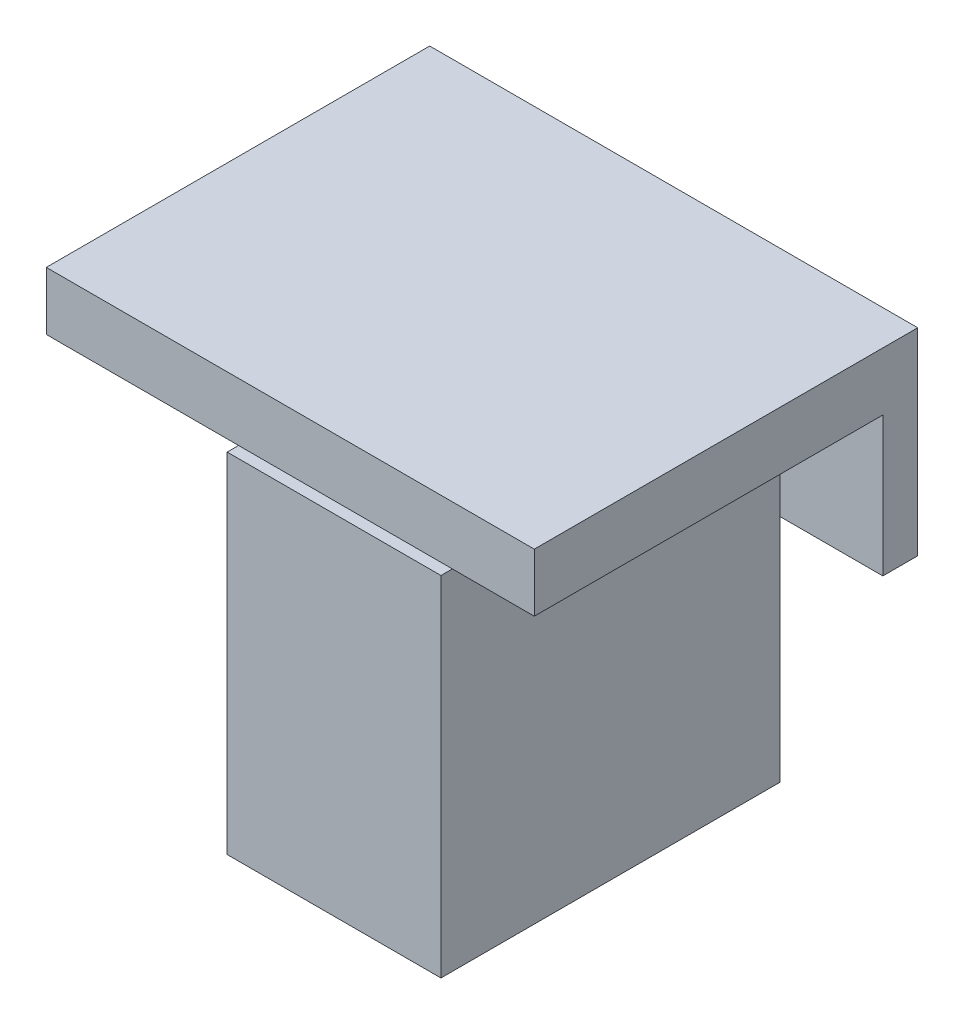
SolidWorks part; units mm, degrees
ref_plane "Plan de face" through (0, 0, 0) normal (0, 0, 1) x (1, 0, 0)
ref_plane "Plan de dessus" through (0, 0, 0) normal (0, 1, 0) x (1, 0, 0)
ref_plane "Plan de droite" through (0, 0, 0) normal (1, 0, 0) x (0, 0, -1)
sketch "Esquisse1" plane through (0, 0, 0) normal (0, 0, 1) x (1, 0, 0)
  line L1 (0, 0) -> (42, 0)
  line L2 (0, 0) -> (0, -17)
  line L3 (0, -17) -> (42, -17)
  line L4 (42, 0) -> (42, -17)
  dimension "D1" = 42
  dimension "D2" = 17
extrude "Boss.-Extru.1" add sketch "Esquisse1" along normal blind 3
sketch "Esquisse2" plane through (0, 0, 3) normal (0, 0, 1) x (1, 0, 0)
  line L0 (0, 0) -> (0, -17) construction
  circle A0 centre (6, -8.5) radius 1.625
  circle A1 centre (36, -8.5) radius 1.625
  point P4 (0, 0)
  point P5 (0, 0)
  point P6 (1.5101, -3.3742)
  point P9 (0, -8.5)
  dimension "D1" = 3.25
  dimension "D2" = 3.25
  dimension "D3" = 30
  dimension "D4" = 6
extrude "Enlèv. mat.-Extru.1" cut sketch "Esquisse2" against normal through all
sketch "Esquisse3" plane through (0, 0, 3) normal (0, 0, 1) x (1, 0, 0)
  line L0 (0, 0) -> (0, -17) construction
  line L1 (42, 0) -> (0, 0)
  line L2 (42, 0) -> (42, -5)
  line L3 (42, -5) -> (0, -5)
  line L4 (0, 0) -> (0, -5)
  dimension "D1" = 5
extrude "Boss.-Extru.2" add sketch "Esquisse3" along normal blind 30
sketch "Esquisse4" plane through (0, -5, 0) normal (0, -1, 0) x (1, 0, 0)
  line L1 (31.9498, 7.7827) -> (19.5498, 7.7827)
  line L2 (31.9498, 7.7827) -> (31.9498, 30.9827)
  line L3 (31.9498, 30.9827) -> (19.5498, 30.9827)
  line L4 (19.5498, 7.7827) -> (19.5498, 30.9827)
  line L5 (34.9498, 4.7827) -> (16.5498, 4.7827)
  line L6 (34.9498, 4.7827) -> (34.9498, 33.9827)
  line L7 (34.9498, 33.9827) -> (16.5498, 33.9827)
  line L8 (16.5498, 4.7827) -> (16.5498, 33.9827)
  dimension "D1" = 3
  dimension "D2" = 3
  dimension "D3" = 3
  dimension "D4" = 3
  dimension "D5" = 12.4
  dimension "D6" = 23.2
extrude "Boss.-Extru.3" add sketch "Esquisse4" along normal blind 30
